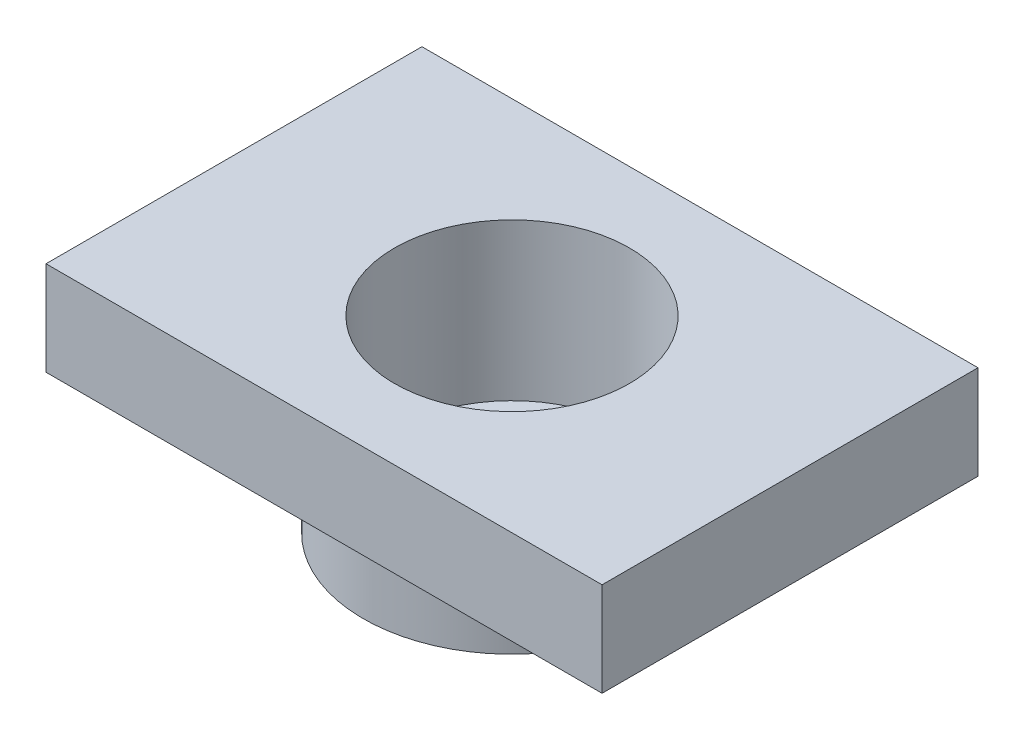
SolidWorks part; units mm, degrees
ref_plane "Plan de face" through (0, 0, 0) normal (0, 0, 1) x (1, 0, 0)
ref_plane "Plan de dessus" through (0, 0, 0) normal (0, 1, 0) x (1, 0, 0)
ref_plane "Plan de droite" through (0, 0, 0) normal (1, 0, 0) x (0, 0, -1)
sketch "Esquisse1" plane through (0, 0, 0) normal (0, 0, 1) x (1, 0, 0)
  line L0 (0, 0) -> (0, -20) construction
  line L1 (19, -12) -> (59, -12)
  line L2 (15, -20) -> (15, 0)
  line L3 (15, -20) -> (9, -20)
  line L5 (59, 0) -> (59, -12)
  line L6 (9, -24) -> (19, -24)
  line L7 (9, -20) -> (9, -24)
  line L9 (19, -24) -> (19, -12)
  line L10 (59, 0) -> (15, 0)
  dimension "D1" = 20
  dimension "D2" = 10
  dimension "D3" = 6
  dimension "D4" = 9
  dimension "D5" = 59
  dimension "D6" = 12
  dimension "D7" = 12
revolve "Révolution1" add sketch "Esquisse1" angle 360 about L0
sketch "Esquisse4" plane through (0, -24, 0) normal (0, -1, 0) x (1, 0, 0)
  line L0 (0, 0) -> (0, 13) construction
  circle A0 centre (0, 13) radius 1.5
  circle A1 centre (13, 0) radius 1.5
  circle A2 centre (0, -13) radius 1.5
  circle A3 centre (-13, 0) radius 1.5
  dimension "D1" = 3
  dimension "D2" = 13
  dimension "D3" = 13
  dimension "D4" = 13
extrude "Extrusion3" cut sketch "Esquisse4" against normal through all
sketch "Esquisse5" plane through (0, -12, 0) normal (0, -1, 0) x (1, 0, 0)
  line L0 (0, 13) -> (13, 0) construction
  line L1 (0, 0) -> (-35.5, 0) construction
  line L2 (-35.5, -24) -> (-35.5, 24)
  line L3 (0, 0) -> (0, -24) construction
  line L4 (35.5, -24) -> (35.5, 24)
  line L5 (35.5, 24) -> (-35.5, 24)
  line L6 (35.5, -24) -> (-35.5, -24)
  dimension "D1" = 48
  dimension "D2" = 71
  dimension "D3" = 35.5
extrude "Extrusion4" cut sketch "Esquisse5" against normal through all flip side to cut
